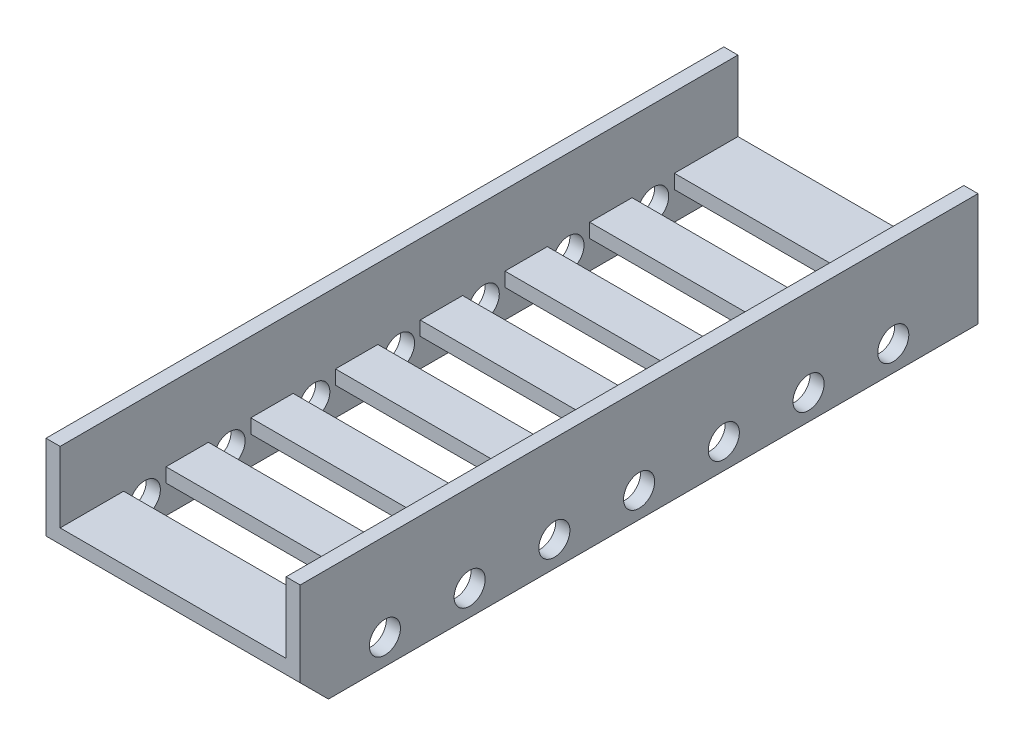
SolidWorks part; units mm, degrees
ref_plane "前视基准面" through (0, 0, 0) normal (0, 0, 1) x (1, 0, 0)
ref_plane "上视基准面" through (0, 0, 0) normal (0, 1, 0) x (1, 0, 0)
ref_plane "右视基准面" through (0, 0, 0) normal (1, 0, 0) x (0, 0, -1)
sketch "草图1" plane through (0, 0, 0) normal (0, 0, 1) x (1, 0, 0)
  line L0 (40, 0) -> (-40, 0)
  line L1 (-40, 0) -> (-40, 25)
  line L2 (-40, 25) -> (-45, 25)
  line L3 (-45, 25) -> (-45, -5)
  line L4 (-45, -5) -> (45, -5)
  line L5 (0, -5) -> (0, 0)
  line L6 (45, 25) -> (45, -5)
  line L7 (40, 25) -> (45, 25)
  line L8 (40, 0) -> (40, 25)
  line L9 (-45, -5) -> (-45, -15)
  line L10 (-45, -15) -> (-40, -15)
  line L11 (-40, -15) -> (-40, -5)
  line L12 (45, -5) -> (45, -15)
  line L13 (40, -15) -> (40, -5)
  line L14 (45, -15) -> (40, -15)
  dimension "D1" = 45
  dimension "D2" = 40
  dimension "D3" = 5
  dimension "D4" = 30
  dimension "D5" = 5
  dimension "D6" = 10
  dimension "D7" = 5
extrude "凸台-拉伸1" add sketch "草图1" along normal blind 240 contours L4 L5 L0 L1 L2 L3 | L8 L0 L5 L4 L6 L7 | L10 L11 L4 L9 | L14 L12 L4 L13
sketch "草图3" plane through (40, 0, 0) normal (-1, 0, 0) x (0, 0, 1)
  line L1 (240, -5) -> (230, -15)
  line L2 (240, -15) -> (0, -15) construction
  line L3 (230, -15) -> (240, -15)
  line L4 (240, -15) -> (240, -5)
  line L5 (120, -6) -> (120, -15)
  circle A0 centre (30, -6) radius 5.5
  circle A1 centre (60, -6) radius 5.5
  circle A2 centre (90, -6) radius 5.5
  circle A3 centre (120, -6) radius 5.5
  circle A4 centre (150, -6) radius 5.5
  circle A5 centre (180, -6) radius 5.5
  circle A6 centre (210, -6) radius 5.5
  point P0 (30, -6)
  point P1 (60, -6)
  point P4 (90, -6)
  point P5 (120, -6)
  point P24 (150, -6)
  point P25 (180, -6)
  point P26 (210, -6)
  dimension "D1" = 9
  dimension "D2" = 30
  dimension "D3" = 30
  dimension "D4" = 30
  dimension "D5" = 10
extrude "切除-拉伸1" cut sketch "草图3" along normal mid plane 180 contours L1 L3 L4 | A6 | A5 | A4 | A3 | A2 | A1 | A0
sketch "草图5" plane through (-40, 0, 0) normal (1, 0, 0) x (0, 0, -1)
  line L0 (-240, -5) -> (0, -5)
  line L1 (0, 25) -> (0, -15) construction
  line L2 (-120, -5) -> (-120, -15)
  line L3 (-217.5, -12.5) -> (-202.5, -12.5)
  line L4 (-217.5, -12.5) -> (-217.5, 2.5)
  line L5 (-217.5, 2.5) -> (-202.5, 2.5)
  line L6 (-202.5, -12.5) -> (-202.5, 2.5)
  line L7 (-210, 2.5) -> (-210, -12.5) construction
  line L8 (-217.5, -5) -> (-202.5, -5) construction
  line L9 (-187.5, -12.5) -> (-172.5, -12.5)
  line L10 (-187.5, -12.5) -> (-187.5, 2.5)
  line L11 (-187.5, 2.5) -> (-172.5, 2.5)
  line L12 (-172.5, -12.5) -> (-172.5, 2.5)
  line L13 (-180, 2.5) -> (-180, -12.5) construction
  line L14 (-187.5, -5) -> (-172.5, -5) construction
  line L15 (-157.5, -12.5) -> (-142.5, -12.5)
  line L16 (-157.5, -12.5) -> (-157.5, 2.5)
  line L17 (-157.5, 2.5) -> (-142.5, 2.5)
  line L18 (-142.5, -12.5) -> (-142.5, 2.5)
  line L19 (-150, 2.5) -> (-150, -12.5) construction
  line L20 (-157.5, -5) -> (-142.5, -5) construction
  line L21 (-127.5, -12.5) -> (-112.5, -12.5)
  line L22 (-127.5, -12.5) -> (-127.5, 2.5)
  line L23 (-127.5, 2.5) -> (-112.5, 2.5)
  line L24 (-112.5, -12.5) -> (-112.5, 2.5)
  line L25 (-120, 2.5) -> (-120, -12.5) construction
  line L26 (-127.5, -5) -> (-112.5, -5) construction
  line L29 (-82.5, 2.5) -> (-97.5, 2.5)
  line L30 (-82.5, -12.5) -> (-97.5, -12.5)
  line L31 (-97.5, -12.5) -> (-97.5, 2.5)
  line L32 (-82.5, -12.5) -> (-82.5, 2.5)
  line L33 (-52.5, 2.5) -> (-67.5, 2.5)
  line L34 (-67.5, -12.5) -> (-67.5, 2.5)
  line L35 (-52.5, -12.5) -> (-67.5, -12.5)
  line L36 (-52.5, -12.5) -> (-52.5, 2.5)
  line L37 (-37.5, -12.5) -> (-37.5, 2.5)
  line L38 (-22.5, -12.5) -> (-37.5, -12.5)
  line L39 (-22.5, -12.5) -> (-22.5, 2.5)
  line L40 (-22.5, 2.5) -> (-37.5, 2.5)
  point P5 (-210, -5)
  point P6 (-180, -5)
  point P7 (-150, -5)
  point P8 (-120, -5)
  point P9 (-180, -5)
  point P10 (-210, -5)
  point P17 (-150, -5)
  point P21 (-120, -5)
  arc M7 (-24.5917, -5) -> (-35.4083, -5) centre (-30, -6) cw
  line M8 (-35.4083, -5) -> (-54.5917, -5)
  arc M9 (-54.5917, -5) -> (-65.4083, -5) centre (-60, -6) cw
  line M10 (-65.4083, -5) -> (-84.5917, -5)
  arc M11 (-84.5917, -5) -> (-95.4083, -5) centre (-90, -6) cw
  line M12 (-95.4083, -5) -> (-114.5917, -5)
  arc M13 (-114.5917, -5) -> (-125.4083, -5) centre (-120, -6) cw
  line M14 (-125.4083, -5) -> (-144.5917, -5)
  dimension "D1" = 30
  dimension "D2" = 30
  dimension "D3" = 30
  dimension "D4" = 30
  dimension "D5" = 120
  dimension "D6" = 15
  dimension "D7" = 15
  dimension "D8" = 15
  dimension "D9" = 15
  dimension "D10" = 15
  dimension "D11" = 15
extrude "切除-拉伸2" cut sketch "草图5" along normal blind 80 contours L0 L6 L5 L4 M14 | L0 L12 L11 L10 M12 | L0 L18 L17 L16 M10 | L0 L24 L23 L22 M8 | L3 L6 L0 L4 M13 M14 | L9 L12 L0 L10 M11 M12 | L15 L18 L0 L16 M9 M10 | L21 L24 L0 L22 M7 M8 | L29 L31 L30 L32 | L33 L34 L35 L36 | L37 L40 L39 L38
